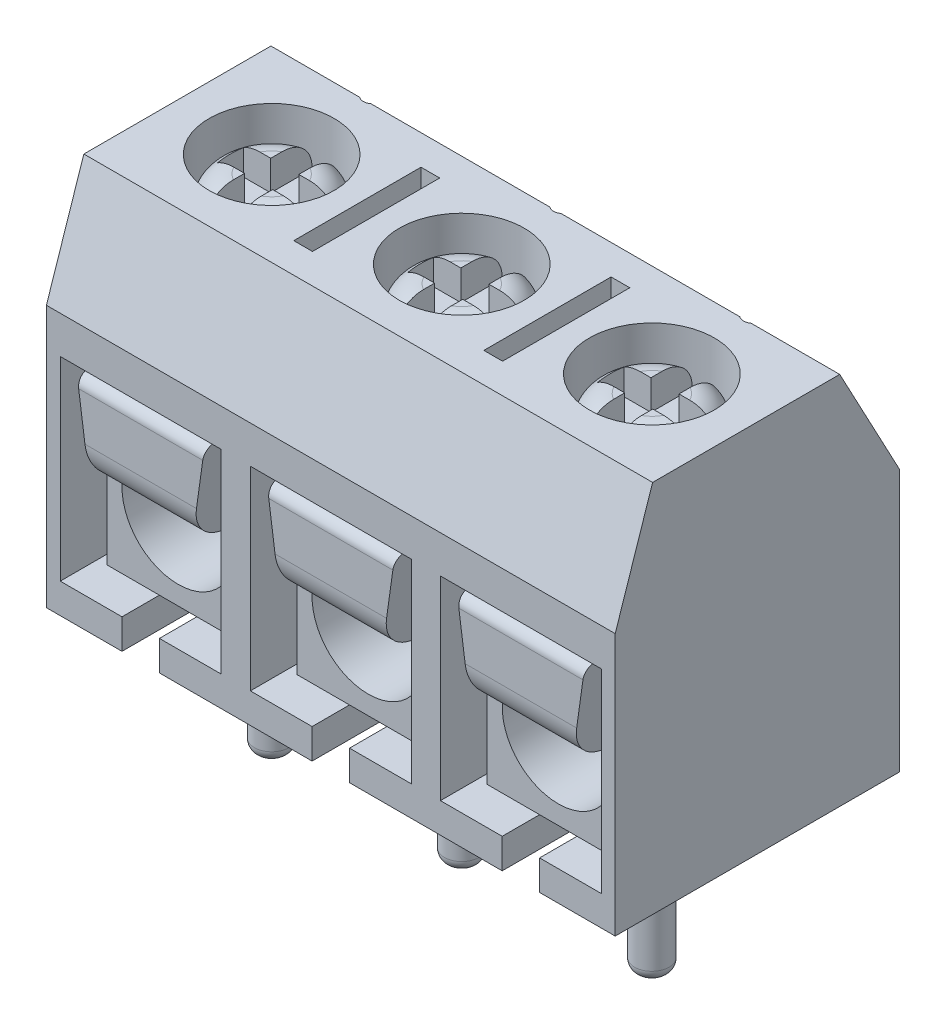
SolidWorks part; units mm, degrees
other "Metal"
other "Plastic"
ref_plane "Front Plane" through (0, 0, 0) normal (0, 0, 1) x (1, 0, 0)
ref_plane "Top Plane" through (0, 0, 0) normal (0, 1, 0) x (1, 0, 0)
ref_plane "Right Plane" through (0, 0, 0) normal (1, 0, 0) x (0, 0, -1)
sketch "Sketch1" plane through (0, 0, 0) normal (1, 0, 0) x (0, 0, -1)
  line L0 (-3.5, 0) -> (4.1, 0)
  line L1 (-3.5, 0) -> (-3.5, 7)
  line L2 (4.1, 0) -> (4.1, 7)
  line L3 (0, 0) -> (0, 10) construction
  line L4 (-2.5, 10) -> (2.5, 10)
  line L5 (4.1, 7) -> (2.5, 10)
  line L6 (-3.5, 7) -> (-2.5, 10)
  dimension "D1" = 3.5
  dimension "D2" = 7.6
  dimension "D3" = 5
  dimension "D4" = 10
  dimension "D5" = 7
extrude "Boss-Extrude1" add sketch "Sketch1" along normal mid plane 15.2
sketch "Sketch3" plane through (0, 10, 0) normal (0, 1, 0) x (1, 0, 0)
  line L0 (-5.08, 0) -> (5.08, 0) construction
  circle A0 centre (0, 0) radius 1.67
  circle A1 centre (-5.08, 0) radius 1.67
  circle A2 centre (5.08, 0) radius 1.67
  dimension "D1" = 3.34
  dimension "D2" = 10.16
extrude "Cut-Extrude1" cut sketch "Sketch3" against normal blind 1.75
sketch "Sketch4" plane through (0, 10, 0) normal (0, 1, 0) x (1, 0, 0)
  line L0 (0, 0) -> (-1.67, 0) construction
  line L1 (-1.67, 0) -> (-3.41, 0) construction
  line L2 (0, 0) -> (1.67, 0) construction
  line L3 (1.67, 0) -> (3.41, 0) construction
  line L4 (-5.08, 0) -> (-3.41, 0) construction
  line L5 (-2.79, 1.7) -> (-2.29, 1.7)
  line L6 (-2.79, 1.7) -> (-2.79, -1.7)
  line L7 (-2.79, -1.7) -> (-2.29, -1.7)
  line L8 (-2.29, 1.7) -> (-2.29, -1.7)
  line L9 (-2.79, 1.7) -> (-2.29, -1.7) construction
  line L10 (-2.79, -1.7) -> (-2.29, 1.7) construction
  line L11 (2.29, 1.7) -> (2.79, 1.7)
  line L12 (2.29, 1.7) -> (2.29, -1.7)
  line L13 (2.29, -1.7) -> (2.79, -1.7)
  line L14 (2.79, 1.7) -> (2.79, -1.7)
  line L15 (2.29, 1.7) -> (2.79, -1.7) construction
  line L16 (2.29, -1.7) -> (2.79, 1.7) construction
  line L17 (5.08, 0) -> (3.41, 0) construction
  line L18 (-5.08, 0) -> (-5.08, 2.7) construction
  line L19 (0, 0) -> (0, 2.7) construction
  line L20 (5.08, 0) -> (5.08, 2.7) construction
  circle A0 centre (0, 0) radius 1.67 construction
  circle A1 centre (-5.08, 0) radius 1.67 construction
  circle A2 centre (-5.08, 0) radius 1.67 construction
  circle A3 centre (0, 0) radius 1.67 construction
  circle A4 centre (5.08, 0) radius 1.67 construction
  circle A5 centre (0, 2.7) radius 0.25
  circle A6 centre (5.08, 2.7) radius 0.25
  circle A7 centre (-5.08, 2.7) radius 0.25
  point P5 (-2.54, 0)
  point P22 (2.54, 0)
  dimension "D3" = 0.5
  dimension "D1" = 3.4
  dimension "D2" = 0.5
  dimension "D4" = 2.7
extrude "Cut-Extrude2" cut sketch "Sketch4" against normal blind 2
sketch "Sketch5" plane through (0, 0, 3.5) normal (0, 0, 1) x (1, 0, 0)
  line L0 (0, 0) -> (0, 0.8) construction
  line L1 (0, 6) -> (0, 10) construction
  line L2 (-2.15, 6) -> (2.15, 6)
  line L3 (-2.15, 6) -> (-2.15, 0.8)
  line L4 (-2.15, 0.8) -> (2.15, 0.8)
  line L5 (2.15, 6) -> (2.15, 0.8)
  line L6 (7.6, 10) -> (-7.6, 10) construction
  line L7 (0, 6) -> (0, 0.8) construction
  line L8 (-5.08, 0) -> (5.08, 0) construction
  line L9 (5.08, 0) -> (5.08, 0.8) construction
  line L10 (-5.08, 0) -> (-5.08, 0.8) construction
  line L12 (-7.23, 6) -> (-2.93, 6)
  line L13 (-7.23, 6) -> (-7.23, 0.8)
  line L14 (-7.23, 0.8) -> (-2.93, 0.8)
  line L15 (-2.93, 6) -> (-2.93, 0.8)
  line L16 (2.93, 6) -> (7.23, 6)
  line L17 (2.93, 6) -> (2.93, 0.8)
  line L18 (2.93, 0.8) -> (7.23, 0.8)
  line L19 (7.23, 6) -> (7.23, 0.8)
  dimension "D4" = 10.16
  dimension "D1" = 4.3
  dimension "D2" = 4
  dimension "D3" = 0.8
extrude "Cut-Extrude3" cut sketch "Sketch5" against normal blind 6
sketch "Sketch6" plane through (0, 0, 0) normal (0, -1, 0) x (1, 0, 0)
  line L0 (0, 0) -> (0, 3.5) construction
  line L1 (7.6, 3.5) -> (-7.6, 3.5) construction
  line L2 (-0.5, 0) -> (-0.5, 3.5)
  line L3 (0.5, 0) -> (0.5, 3.5)
  line L4 (0, 3.5) -> (0, 4) construction
  line L5 (0, 0) -> (0, -0.5) construction
  line L6 (-5.08, 0) -> (5.08, 0) construction
  line L7 (-5.08, 0) -> (-5.08, 3.5) construction
  line L8 (-5.58, 0) -> (-5.58, 3.5)
  line L9 (-4.58, 0) -> (-4.58, 3.5)
  line L10 (5.08, 0) -> (5.08, 3.5) construction
  line L11 (4.58, 0) -> (4.58, 3.5)
  line L12 (5.58, 0) -> (5.58, 3.5)
  arc A0 (-0.5, 0) -> (0.5, 0) centre (0, 0) ccw
  arc A1 (0.5, 3.5) -> (-0.5, 3.5) centre (0, 3.5) ccw
  arc A2 (-5.58, 0) -> (-4.58, 0) centre (-5.08, 0) ccw
  arc A3 (-4.58, 3.5) -> (-5.58, 3.5) centre (-5.08, 3.5) ccw
  arc A4 (4.58, 0) -> (5.58, 0) centre (5.08, 0) ccw
  arc A5 (5.58, 3.5) -> (4.58, 3.5) centre (5.08, 3.5) ccw
  point P5 (0, 1.75)
  point P16 (-5.08, 1.75)
  point P22 (5.08, 1.75)
  dimension "D1" = 10.16
  dimension "D2" = 1
extrude "Cut-Extrude4" cut sketch "Sketch6" against normal up to surface (0.8 mm away) up to face at (0, 0.8, 0.5)
sketch "Sketch9" plane through (0, 8.25, 0) normal (0, 1, 0) x (1, 0, 0)
  circle A0 centre (0, 0) radius 1.5
  circle A1 centre (5.08, 0) radius 1.5
  circle A2 centre (-5.08, 0) radius 1.5
  dimension "D1" = 3
extrude "Boss-Extrude5" add sketch "Sketch9" along normal blind 1.3
fillet "Fillet1" radius 0.75 3 edges at (5.08, 9.55, 1.5) (0, 9.55, 1.5) (-5.08, 9.55, 1.5)
sketch "Sketch10" plane through (0, 9.55, 0) normal (0, 1, 0) x (1, 0, 0)
  line L1 (-0.375, 1.55) -> (0.375, 1.55)
  line L2 (-0.375, 1.55) -> (-0.375, -1.55)
  line L3 (-0.375, -1.55) -> (0.375, -1.55)
  line L4 (0.375, 1.55) -> (0.375, -1.55)
  line L5 (-0.375, 1.55) -> (0.375, -1.55) construction
  line L6 (-0.375, -1.55) -> (0.375, 1.55) construction
  line L7 (-5.455, 1.55) -> (-4.705, 1.55)
  line L8 (-5.455, 1.55) -> (-5.455, -1.55)
  line L9 (-5.455, -1.55) -> (-4.705, -1.55)
  line L10 (-4.705, 1.55) -> (-4.705, -1.55)
  line L11 (-5.455, 1.55) -> (-4.705, -1.55) construction
  line L12 (-5.455, -1.55) -> (-4.705, 1.55) construction
  line L13 (4.705, 1.55) -> (5.455, 1.55)
  line L14 (4.705, 1.55) -> (4.705, -1.55)
  line L15 (4.705, -1.55) -> (5.455, -1.55)
  line L16 (5.455, 1.55) -> (5.455, -1.55)
  line L17 (4.705, 1.55) -> (5.455, -1.55) construction
  line L18 (4.705, -1.55) -> (5.455, 1.55) construction
  point P0 (0, 0)
  point P5 (-5.08, 0)
  point P11 (5.08, 0)
  dimension "D1" = 0.75
  dimension "D2" = 3.1
extrude "Cut-Extrude5" cut sketch "Sketch10" against normal blind 0.8
sketch "Sketch11" plane through (0, 9.55, 0) normal (0, 1, 0) x (1, 0, 0)
  line L1 (-1.1, 0.35) -> (1.1, 0.35)
  line L2 (-1.1, 0.35) -> (-1.1, -0.35)
  line L3 (-1.1, -0.35) -> (1.1, -0.35)
  line L4 (1.1, 0.35) -> (1.1, -0.35)
  line L5 (-1.1, 0.35) -> (1.1, -0.35) construction
  line L6 (-1.1, -0.35) -> (1.1, 0.35) construction
  line L7 (-6.18, 0.35) -> (-3.98, 0.35)
  line L8 (-6.18, 0.35) -> (-6.18, -0.35)
  line L9 (-6.18, -0.35) -> (-3.98, -0.35)
  line L10 (-3.98, 0.35) -> (-3.98, -0.35)
  line L11 (-6.18, 0.35) -> (-3.98, -0.35) construction
  line L12 (-6.18, -0.35) -> (-3.98, 0.35) construction
  line L13 (3.98, 0.35) -> (6.18, 0.35)
  line L14 (3.98, 0.35) -> (3.98, -0.35)
  line L15 (3.98, -0.35) -> (6.18, -0.35)
  line L16 (6.18, 0.35) -> (6.18, -0.35)
  line L17 (3.98, 0.35) -> (6.18, -0.35) construction
  line L18 (3.98, -0.35) -> (6.18, 0.35) construction
  point P0 (0, 0)
  point P5 (-5.08, 0)
  point P11 (5.08, 0)
  dimension "D1" = 2.2
  dimension "D2" = 0.7
extrude "Cut-Extrude6" cut sketch "Sketch11" against normal up to surface (0.8 mm away) up to face at (-5.08, 8.75, 0)
sketch "Sketch7" plane through (0, 0, -2.5) normal (0, 0, 1) x (1, 0, 0)
  line L0 (-7.23, 6) -> (-7.23, 0.8) construction
  line L1 (-7.23, 6) -> (7.23, 6)
  line L2 (-7.23, 6) -> (-7.23, 0.8)
  line L3 (-7.23, 0.8) -> (7.23, 0.8)
  line L4 (7.23, 6) -> (7.23, 0.8)
  line L5 (-2.93, 6) -> (-7.23, 6) construction
  line L6 (-2.93, 6) -> (-7.23, 6) construction
extrude "Boss-Extrude3" add sketch "Sketch7" along normal blind 0.5 separate body
sketch "Sketch8" plane through (0, 0, -2) normal (0, 0, 1) x (1, 0, 0)
  line L0 (-5.08, 0) -> (5.08, 0) construction
  line L1 (-5.08, 0) -> (-5.08, 0.8) construction
  line L2 (-4.58, 0.8) -> (-5.58, 0.8) construction
  line L3 (5.08, 0) -> (5.08, 0.8) construction
  line L4 (5.58, 0.8) -> (4.58, 0.8) construction
  line L5 (0, 0) -> (0, 0.8) construction
  line L6 (0.5, 0.8) -> (-0.5, 0.8) construction
  line L7 (0, 0.8) -> (0, 2.8) construction
  line L8 (-6.98, 5.8) -> (-3.18, 5.8)
  line L9 (-6.98, 5.8) -> (-6.98, 0.8)
  line L10 (-6.98, 0.8) -> (-3.18, 0.8)
  line L11 (-3.18, 5.8) -> (-3.18, 0.8)
  line L12 (-1.9, 5.8) -> (1.9, 5.8)
  line L13 (-1.9, 5.8) -> (-1.9, 0.8)
  line L14 (-1.9, 0.8) -> (1.9, 0.8)
  line L15 (1.9, 5.8) -> (1.9, 0.8)
  line L16 (3.18, 5.8) -> (6.98, 5.8)
  line L17 (3.18, 5.8) -> (3.18, 0.8)
  line L18 (3.18, 0.8) -> (6.98, 0.8)
  line L19 (6.98, 5.8) -> (6.98, 0.8)
  line L20 (0, 2.8) -> (0, 5.8) construction
  line L21 (-5.08, 0.8) -> (-5.08, 2.8) construction
  line L22 (-5.08, 2.8) -> (-5.08, 5.8) construction
  line L23 (5.08, 0.8) -> (5.08, 2.8) construction
  line L24 (5.08, 2.8) -> (5.08, 5.8) construction
  circle A0 centre (-5.08, 2.8) radius 1.5
  circle A1 centre (0, 2.8) radius 1.5
  circle A2 centre (5.08, 2.8) radius 1.5
  dimension "D4" = 3
  dimension "D1" = 3.8
  dimension "D2" = 5
  dimension "D3" = 2
extrude "Boss-Extrude4" add sketch "Sketch8" along normal offset from surface (4.5 mm away) 1 up to face at (0, 2.1286, 3.5)
fillet "Fillet2" radius 0.2 6 edges at (6.98, 5.8, 0.25) (3.18, 5.8, 0.25) (1.9, 5.8, 0.25) (-1.9, 5.8, 0.25) (-3.18, 5.8, 0.25) (-6.98, 5.8, 0.25)
sketch "Sketch12" plane through (0, 0, 3.5) normal (0, 0, 1) x (1, 0, 0)
  line L0 (0, 2.8) -> (0, 3.3) construction
  line L1 (1.35, 3.3) -> (-1.35, 3.3)
  line L2 (0, 3.3) -> (0, 5.8) construction
  line L3 (-1.7, 5.8) -> (1.7, 5.8) construction
  line L4 (-1.7, 5.8) -> (1.7, 5.8)
  line L5 (-1.7, 5.8) -> (-1.35, 3.3)
  line L6 (1.7, 5.8) -> (1.35, 3.3)
  line L7 (5.08, 2.8) -> (5.08, 3.3) construction
  line L8 (5.08, 3.3) -> (5.08, 5.8) construction
  line L9 (3.38, 5.8) -> (6.78, 5.8) construction
  line L10 (-5.08, 2.8) -> (-5.08, 3.3) construction
  line L11 (-5.08, 3.3) -> (-5.08, 5.8) construction
  line L12 (-6.78, 5.8) -> (-3.38, 5.8) construction
  line L13 (-6.78, 5.8) -> (-3.38, 5.8)
  line L14 (3.38, 5.8) -> (6.78, 5.8)
  line L15 (-6.43, 3.3) -> (-3.73, 3.3)
  line L16 (3.73, 3.3) -> (6.43, 3.3)
  line L17 (-6.43, 3.3) -> (-6.78, 5.8)
  line L18 (-3.73, 3.3) -> (-3.38, 5.8)
  line L19 (3.73, 3.3) -> (3.38, 5.8)
  line L20 (6.43, 3.3) -> (6.78, 5.8)
  dimension "D1" = 2.7
  dimension "D2" = 2.5
extrude "Boss-Extrude6" add sketch "Sketch12" against normal up to surface (5.5 mm away) up to face at (1.5, 2.8, -2)
fillet "Fillet3" radius 1 3 edges at (5.08, 3.3, 3.5) (0, 3.3, 3.5) (-5.08, 3.3, 3.5)
fillet "Fillet4" radius 0.3 3 edges at (5.08, 5.8, 3.5) (0, 5.8, 3.5) (-5.08, 5.8, 3.5)
sketch "Sketch13" plane through (0, 0.8, 0) normal (0, -1, 0) x (1, 0, 0)
  circle A0 centre (0, 0) radius 0.46
  circle A1 centre (5.08, 0) radius 0.46
  circle A2 centre (-5.08, 0) radius 0.46
  dimension "D1" = 0.92
extrude "Boss-Extrude7" add sketch "Sketch13" along normal offset from surface (4.6 mm away) 3.8 up to face at (0, 0, 1.1438) offset beyond the face yes
fillet "Fillet5" radius 0.3 3 edges at (-5.08, -3.8, 0.46) (5.08, -3.8, 0.46) (0, -3.8, 0.46)
